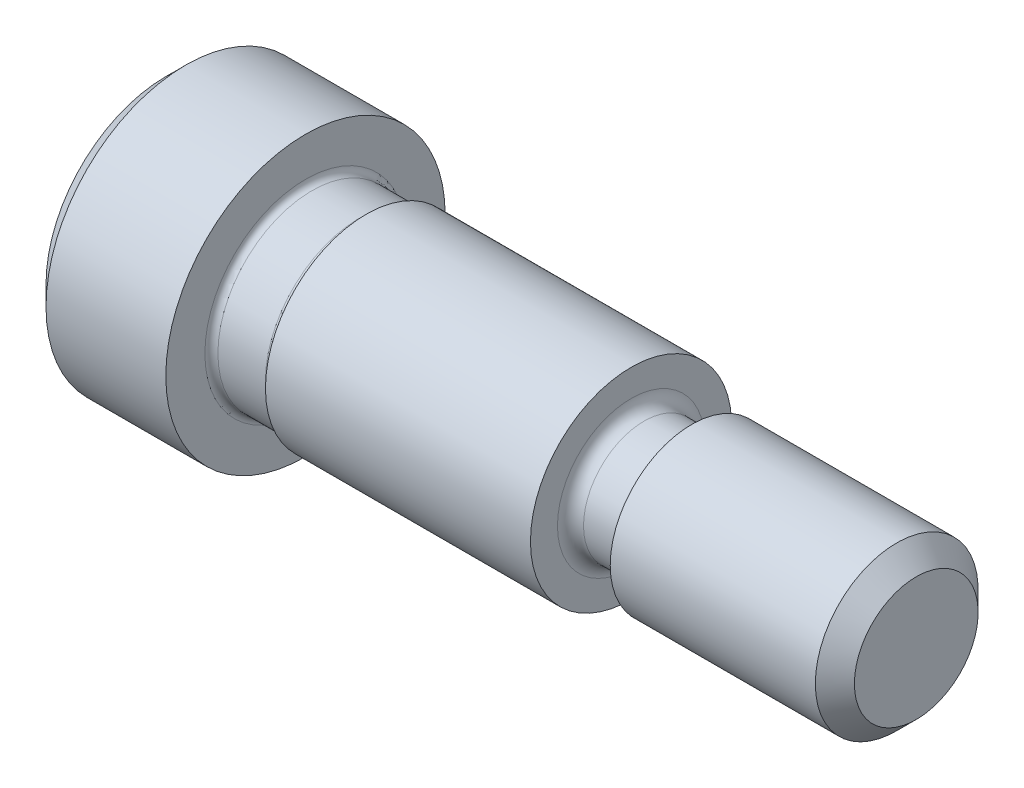
SolidWorks part; units mm, degrees
material "AISI 1020"
ref_plane "Front Plane" through (0, 0, 0) normal (0, 0, 1) x (1, 0, 0)
ref_plane "Top Plane" through (0, 0, 0) normal (0, 1, 0) x (1, 0, 0)
ref_plane "Right Plane" through (0, 0, 0) normal (1, 0, 0) x (0, 0, -1)
sketch "Sketch1" plane through (0, 0, 0) normal (0, 0, 1) x (1, 0, 0)
  line L0 (26.0236, 46.1789) -> (30.6972, 46.1789)
  line L1 (30.6972, 44.9089) -> (30.6972, 44.6549)
  line L2 (25.2616, 45.4169) -> (25.2616, 40.7306)
  line L3 (30.6972, 46.1789) -> (30.6972, 44.9089)
  line L4 (31.2052, 44.4009) -> (32.8054, 44.4009)
  line L5 (30.9512, 44.4009) -> (31.2052, 44.4009)
  line L6 (43.3972, 44.6549) -> (43.3972, 43.6008)
  line L7 (45.7594, 43.9056) -> (53.7604, 43.9056)
  line L11 (43.9052, 43.0928) -> (45.5054, 43.0928)
  line L12 (33.0594, 44.6549) -> (43.3972, 44.6549)
  line L15 (25.2616, 40.7306) -> (54.5224, 40.7306)
  line L20 (45.7594, 43.9056) -> (45.7594, 43.3468)
  line L23 (25.2616, 45.4169) -> (26.0236, 46.1789)
  line L25 (54.5224, 43.1436) -> (54.5224, 40.7306)
  line L26 (53.7604, 43.9056) -> (54.5224, 43.1436)
  arc A0 (30.9512, 44.4009) -> (30.6972, 44.6549) centre (30.9512, 44.6549) cw
  arc A1 (43.3972, 43.6008) -> (43.9052, 43.0928) centre (43.9052, 43.6008) ccw
  arc A4 (32.8054, 44.4009) -> (33.0594, 44.6549) centre (32.8054, 44.6549) ccw
  arc A7 (45.5054, 43.0928) -> (45.7594, 43.3468) centre (45.5054, 43.3468) ccw
  dimension "D1" = 0.254
revolve "Revolve1" add sketch "Sketch1" angle 360 about L15
